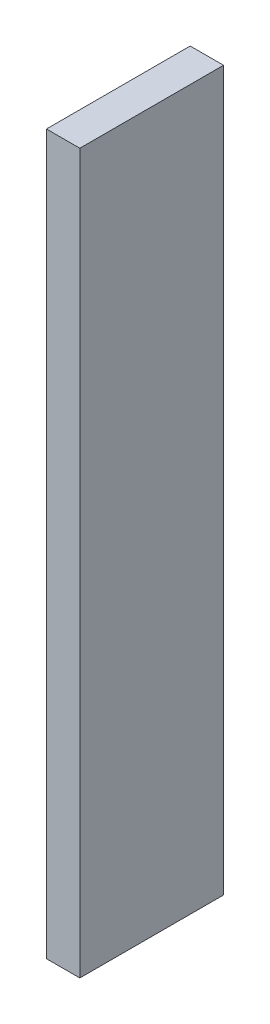
SolidWorks part; units mm, degrees
ref_plane "Front Plane" through (0, 0, 0) normal (0, 0, 1) x (1, 0, 0)
ref_plane "Top Plane" through (0, 0, 0) normal (0, 1, 0) x (1, 0, 0)
ref_plane "Right Plane" through (0, 0, 0) normal (1, 0, 0) x (0, 0, -1)
sketch "Sketch1" plane through (0, 0, 0) normal (0, 0, 1) x (1, 0, 0)
  line L0 (-39, -62.5) -> (39, -62.5) construction
  line L1 (-39, 62.5) -> (-33.2, 62.5)
  line L2 (-39, 62.5) -> (-39, -62.5)
  line L3 (-39, -62.5) -> (-33.2, -62.5)
  line L4 (-33.2, 62.5) -> (-33.2, -62.5)
  dimension "D1" = 5.8
extrude "Boss-Extrude1" add sketch "Sketch1" along normal up to surface (25 mm away)
